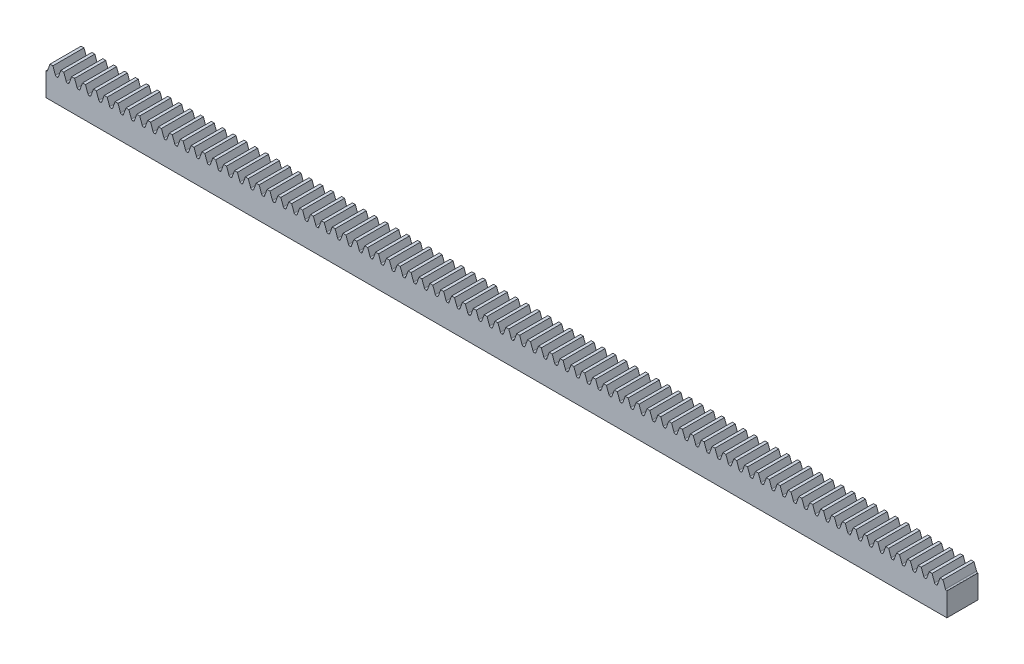
SolidWorks part; units mm, degrees
material "Acier allié"
ref_plane "Plan median" through (0, 0, 0) normal (0, 0, 1) x (1, 0, 0)
ref_plane "Plan2" through (0, 0, 0) normal (0, 1, 0) x (1, 0, 0)
ref_plane "Plan3" through (0, 0, 0) normal (1, 0, 0) x (0, 0, -1)
sketch "Esquisse1" plane through (0, 0, 0) normal (0, 0, 1) x (1, 0, 0)
  line L0 (0, 0) -> (1.5708, 0) construction
  line L1 (0.3639, 1) -> (-0.3639, -0.9999)
  line L2 (0.3639, 1) -> (1.2069, 1)
  line L3 (1.2069, 1) -> (1.9347, -0.9999)
  line L4 (0, 0) -> (0, 1) construction
  line L5 (2.2918, -1.25) -> (2.3562, -1.25)
  line L6 (-0.721, -1.25) -> (-0.7854, -1.25)
  line L7 (2.3562, -1.25) -> (2.3562, 1.7854)
  line L8 (-0.7854, -1.25) -> (-0.7854, 1.7854)
  line L9 (-0.7854, 1.7854) -> (2.3562, 1.7854)
  arc A0 (1.9347, -0.9999) -> (2.2918, -1.25) centre (2.2918, -0.87) ccw
  arc A1 (-0.721, -1.25) -> (-0.3639, -0.9999) centre (-0.721, -0.87) ccw
  point P14 (-0.4549, -1.25)
  dimension "R1" = 0.38
  dimension "m" = 1
  dimension "FD" = 1.25
  dimension "LD" = 1.5708
ref_plane "Plan4" through (-0.7854, 0, 0) normal (1, 0, 0) x (0, 0, -1)
sketch "Section Cremaillere" plane through (-0.7854, 0, 0) normal (1, 0, 0) x (0, 0, -1)
  line L1 (-4.5, 1.7854) -> (4.5, 1.7854)
  line L2 (-4.5, 1.7854) -> (-4.5, -8)
  line L3 (-4.5, -8) -> (4.5, -8)
  line L4 (4.5, 1.7854) -> (4.5, -8)
  line L5 (0, -8) -> (0, 1.7854) construction
  line L6 (0, 50) -> (0, -50) construction
  dimension "L" = 9
  dimension "h" = 8
extrude "Base-Extrusion" add sketch "Section Cremaillere" along normal blind 260.7522
extrude "Enlèv. mat.-Extru.2" cut sketch "Esquisse1" against normal through all and the other way blind 100
pattern_linear "Répétition linéaire1" count 83 spacing 3.1416 along (1, 0, 0) of "Enlèv. mat.-Extru.2"
sketch "Esquisse2" plane through (-0.7854, 0, 0) normal (-1, 0, 0) x (0, 0, 1)
  line L0 (0, 0) -> (-4.5, 0)
  line L1 (0, 0) -> (4.5, 0)
  line L2 (-4.5, -1.25) -> (4.5, -1.25) construction
  line L3 (-4.5, -1.25) -> (4.5, -1.25)
  line L4 (-4.5, 1.7854) -> (-4.5, -8) construction
  line L5 (4.5, 1.7854) -> (4.5, -8) construction
  line L6 (-4.5, 0) -> (-4.5, -1.25)
  line L7 (4.5, 0) -> (4.5, -1.25)
extrude "Plan primitif" [suppressed] add sketch "Esquisse2" along normal up to surface (260.7522 mm away)
sketch "Esquisse3" plane through (0, -8, 0) normal (0, -1, 0) x (1, 0, 0)
  line L0 (42.6733, 0) -> (-0.7854, 0) construction
  line L1 (129.5907, 0.2029) -> (129.5907, -73.2029) construction
  line L2 (-0.7854, 4.5) -> (-0.7854, -4.5) construction
  line L3 (216.5081, 0) -> (259.9668, 0) construction
  line L4 (259.9668, 4.5) -> (259.9668, -4.5) construction
  line L5 (-0.7854, 0) -> (42.6733, 0) construction
  line L6 (129.5907, 0) -> (86.132, 0) construction
  line L7 (86.132, 0) -> (42.6733, 0) construction
  circle A0 centre (42.6733, 0) radius 1.65
  circle A1 centre (129.5907, 0) radius 1.65
  circle A2 centre (216.5081, 0) radius 1.65
  point P15 (42.6733, 0)
  dimension "D1" = 3.3
  dimension "D2" = 3
extrude "Enlèv. mat.-Extru.3" cut sketch "Esquisse3" against normal blind 5.5
ref_plane "Plan" through (129.5907, 0, 0) normal (-1, 0, 0) x (0, 0, 1)
sketch "Esquisse4" plane through (0, 0, 4.5) normal (0, 0, 1) x (1, 0, 0)
  line L0 (-0.7854, 0) -> (290.5165, 0)
  line L1 (-0.7854, -1.25) -> (-0.7854, -8) construction
  line L2 (259.9668, -8) -> (-0.7854, -8) construction
  dimension "D1" = 8
equation "\"LD@Esquisse1\" = \"m@Esquisse1\"*1.570796327"
equation "\"FD@Esquisse1\"=\"m@Esquisse1\"*1.25"
equation "\"DLD@Esquisse1\"=\"LD@Esquisse1\"/2"
equation "\"R1@Esquisse1\"=\"m@Esquisse1\"*0.38"
equation "\"D1@Base-Extrusion\"=\"LD@Esquisse1\"*2*\"Nd@Répétition linéaire1\""
equation "\"D3@Répétition linéaire1\"=\"LD@Esquisse1\"*2"
